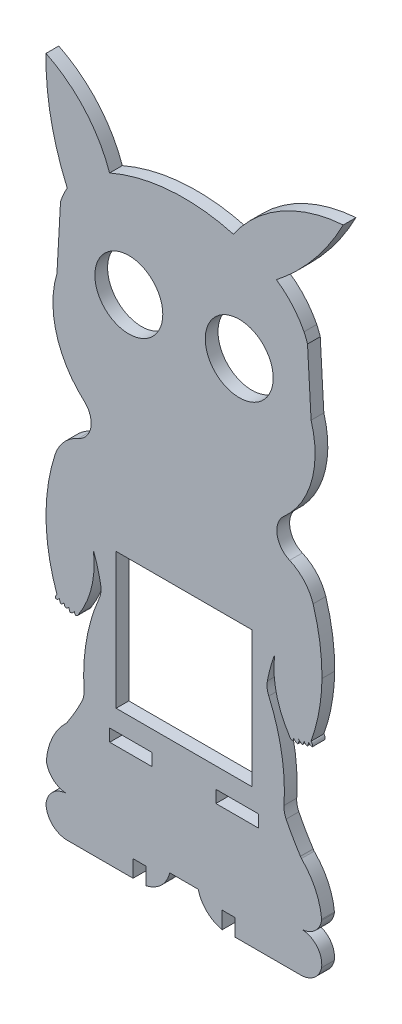
SolidWorks part; units mm, degrees
ref_plane "Alzado" through (0, 0, 0) normal (0, 0, 1) x (1, 0, 0)
ref_plane "Planta" through (0, 0, 0) normal (0, 1, 0) x (1, 0, 0)
ref_plane "Vista lateral" through (0, 0, 0) normal (1, 0, 0) x (0, 0, -1)
sketch "Model" plane through (0, 0, 0) normal (0, 0, 1) x (1, 0, 0)
  line L0 (39.3201, -24.5464) -> (49.3201, -24.5464)
  line L1 (49.3201, -24.5464) -> (49.3201, -21.6464)
  line L2 (49.3201, -21.6464) -> (39.3201, -21.6464)
  line L3 (39.3201, -21.6464) -> (39.3201, -24.5464)
  line L4 (14.3201, -24.5464) -> (24.3201, -24.5464)
  line L5 (24.3201, -24.5464) -> (24.3201, -21.6464)
  line L6 (24.3201, -21.6464) -> (14.3201, -21.6464)
  line L7 (14.3201, -21.6464) -> (14.3201, -24.5464)
  line L8 (32.3201, 15.1316) -> (47.8201, 15.1316)
  line L9 (47.8201, 15.1316) -> (47.8201, -16.8684)
  line L10 (47.8201, -16.8684) -> (15.8201, -16.8684)
  line L11 (15.8201, -16.8684) -> (15.8201, 15.1316)
  line L12 (15.8201, 15.1316) -> (32.3201, 15.1316)
  line L13 (2.7381, 79.9587) -> (1.8933, 64.837)
  line L14 (4.32, -49.5464) -> (19.8201, -49.5464)
  line L15 (19.8201, -49.5464) -> (19.8201, -45.5464)
  line L16 (19.8201, -45.5464) -> (22.8201, -45.5464)
  line L17 (22.8201, -45.5464) -> (22.8201, -49.5464)
  line L18 (28.4714, -44.1146) -> (35.1688, -44.1146)
  line L19 (40.8201, -49.5464) -> (40.8201, -45.5464)
  line L20 (40.8201, -45.5464) -> (43.8201, -45.5464)
  line L21 (43.8201, -45.5464) -> (43.8201, -49.5464)
  line L22 (43.8201, -49.5464) -> (59.3202, -49.5464)
  line L23 (61.7468, 64.837) -> (60.902, 79.9587)
  circle A0 centre (18.8201, 68.9756) radius 8
  circle A1 centre (44.8201, 68.9756) radius 8
  arc A2 (58.5016, 93.7616) -> (69.3188, 108.4536) centre (17.499, 135.2785) ccw
  arc A3 (69.3188, 108.4536) -> (43.4441, 93.6349) centre (71.8737, 73.9934) ccw
  arc A4 (43.4441, 93.6349) -> (14.2885, 91.5406) centre (31.8201, 51.4678) ccw
  arc A5 (14.2885, 91.5406) -> (-0.6812, 108.4536) centre (-13.8302, 81.7341) ccw
  arc A6 (-0.6812, 108.4536) -> (4.3118, 83.4695) centre (58.9217, 107.3742) ccw
  arc A7 (4.3118, 83.4695) -> (2.7381, 79.9587) centre (19.4465, 74.5775) ccw
  arc A8 (1.8933, 64.837) -> (8.49, 41.856) centre (22.9856, 58.4542) ccw
  arc A9 (6.9503, 33.7364) -> (8.49, 41.856) centre (4.9542, 38.3207) ccw
  arc A10 (6.9503, 33.7364) -> (1.4202, 27.6218) centre (10.9425, 24.5679) ccw
  arc A11 (1.4202, 27.6218) -> (1.9033, -0.6441) centre (43.2704, 14.1999) ccw
  arc A12 (1.9033, -0.6441) -> (1.6278, -1.6592) centre (2.4449, -1.3361) ccw
  arc A13 (1.6278, -1.6592) -> (2.468, -1.1028) centre (1.5649, -0.6516) ccw
  arc A14 (2.468, -1.1028) -> (2.8133, -2.0874) centre (4.6346, -0.8959) ccw
  arc A15 (2.8133, -2.0874) -> (3.6029, -1.3726) centre (2.316, -0.7446) ccw
  arc A16 (3.6029, -1.3726) -> (3.9097, -2.306) centre (4.8035, -1.495) ccw
  arc A17 (3.9097, -2.306) -> (4.8112, -1.6539) centre (3.6467, -0.9933) ccw
  arc A18 (4.8112, -1.6539) -> (5.0221, -2.7407) centre (5.9741, -1.9921) ccw
  arc A19 (5.0221, -2.7407) -> (6.0195, -2.0247) centre (4.7112, -1.255) ccw
  arc A20 (6.0195, -2.0247) -> (6.3455, -2.6768) centre (6.6928, -2.0956) ccw
  arc A21 (6.3455, -2.6768) -> (7.0168, -2.0758) centre (6.1854, -1.8226) ccw
  arc A22 (7.0168, -2.0758) -> (10.4808, 12.7306) centre (-11.2939, 10.0165) ccw
  arc A23 (12.1923, 6.5144) -> (10.4808, 12.7306) centre (-25.5016, -0.52) ccw
  arc A24 (11.86, 3.5977) -> (12.1923, 6.5144) centre (7.2772, 5.5971) ccw
  arc A25 (11.86, 3.5977) -> (8.275, -16.9242) centre (52.2813, -14.0377) ccw
  arc A26 (7.7731, -19.4566) -> (8.275, -16.9242) centre (3.2857, -17.2514) ccw
  arc A27 (4.4038, -25.3376) -> (7.7731, -19.4566) centre (-40.1485, 4.0925) ccw
  arc A28 (4.1646, -25.6944) -> (4.4038, -25.3376) centre (3.473, -24.9721) ccw
  arc A29 (4.1646, -25.6944) -> (-0.5995, -35.6873) centre (14.965, -36.9755) ccw
  arc A30 (-0.5995, -35.6873) -> (-0.589, -35.9359) centre (0.3971, -35.7698) ccw
  arc A31 (-0.589, -35.9359) -> (3.9848, -40.0925) centre (4.3415, -35.1052) ccw
  arc A32 (3.9848, -40.0925) -> (-0.68, -44.5463) centre (4.3693, -45.1651) ccw
  arc A33 (-0.68, -44.5463) -> (4.32, -49.5464) centre (4.32, -44.5464) ccw
  arc A34 (22.8201, -49.5464) -> (28.4714, -44.1146) centre (21.3419, -42.3528) ccw
  arc A35 (35.1688, -44.1146) -> (40.8201, -49.5464) centre (42.2982, -42.3528) ccw
  arc A36 (59.3202, -49.5464) -> (64.208, -45.5996) centre (59.3202, -44.5464) ccw
  arc A37 (64.208, -45.5996) -> (59.6553, -40.0925) centre (59.4769, -44.8753) ccw
  arc A38 (59.6553, -40.0925) -> (64.2291, -35.9359) centre (59.2986, -35.1052) ccw
  arc A39 (64.2291, -35.9359) -> (64.2396, -35.6873) centre (63.243, -35.7698) ccw
  arc A40 (64.2396, -35.6873) -> (59.4756, -25.6944) centre (48.0103, -37.2925) ccw
  arc A41 (59.2363, -25.3376) -> (59.4756, -25.6944) centre (60.1671, -24.9721) ccw
  arc A42 (55.867, -19.4566) -> (59.2363, -25.3376) centre (103.7886, 4.0925) ccw
  arc A43 (55.3652, -16.9242) -> (55.867, -19.4566) centre (60.3545, -17.2514) ccw
  arc A44 (55.3652, -16.9242) -> (51.7801, 3.5977) centre (11.3588, -14.0377) ccw
  arc A45 (51.4478, 6.5144) -> (51.7801, 3.5977) centre (56.363, 5.5971) ccw
  arc A46 (53.1593, 12.7306) -> (51.4478, 6.5144) centre (89.1417, -0.52) ccw
  arc A47 (53.1593, 12.7306) -> (56.6233, -2.0758) centre (74.9341, 10.0165) ccw
  arc A48 (56.6233, -2.0758) -> (57.2946, -2.6768) centre (57.4547, -1.8226) ccw
  arc A49 (57.2946, -2.6768) -> (57.6207, -2.0247) centre (56.9473, -2.0956) ccw
  arc A50 (57.6207, -2.0247) -> (58.618, -2.7407) centre (58.929, -1.255) ccw
  arc A51 (58.618, -2.7407) -> (58.829, -1.6539) centre (57.666, -1.9921) ccw
  arc A52 (58.829, -1.6539) -> (59.7304, -2.306) centre (59.9934, -0.9933) ccw
  arc A53 (59.7304, -2.306) -> (60.0373, -1.3726) centre (58.8366, -1.495) ccw
  arc A54 (60.0373, -1.3726) -> (60.8269, -2.0874) centre (61.3241, -0.7446) ccw
  arc A55 (60.8269, -2.0874) -> (61.1721, -1.1028) centre (59.0055, -0.8959) ccw
  arc A56 (61.1721, -1.1028) -> (62.0124, -1.6592) centre (62.0753, -0.6516) ccw
  arc A57 (62.0124, -1.6592) -> (61.7369, -0.6441) centre (61.1952, -1.3361) ccw
  arc A58 (61.7369, -0.6441) -> (64.313, 13.4408) centre (20.3698, 14.1999) ccw
  arc A59 (64.313, 13.4408) -> (62.2199, 27.6218) centre (17.1123, 13.7191) ccw
  arc A60 (62.2199, 27.6218) -> (56.6898, 33.7364) centre (52.6976, 24.5679) ccw
  arc A61 (55.1501, 41.856) -> (56.6898, 33.7364) centre (58.6859, 38.3207) ccw
  arc A62 (55.1501, 41.856) -> (61.7468, 64.837) centre (40.6545, 58.4542) ccw
  arc A63 (60.902, 79.9587) -> (60.0821, 82.0396) centre (44.1937, 74.5775) ccw
  arc A64 (60.0821, 82.0396) -> (53.5736, 89.4147) centre (42.7105, 73.2686) ccw
  arc A65 (53.5736, 89.4147) -> (58.5016, 93.7616) centre (10.5723, 143.1311) ccw
extrude "Saliente-Extruir1" add sketch "Model" along normal blind 3
